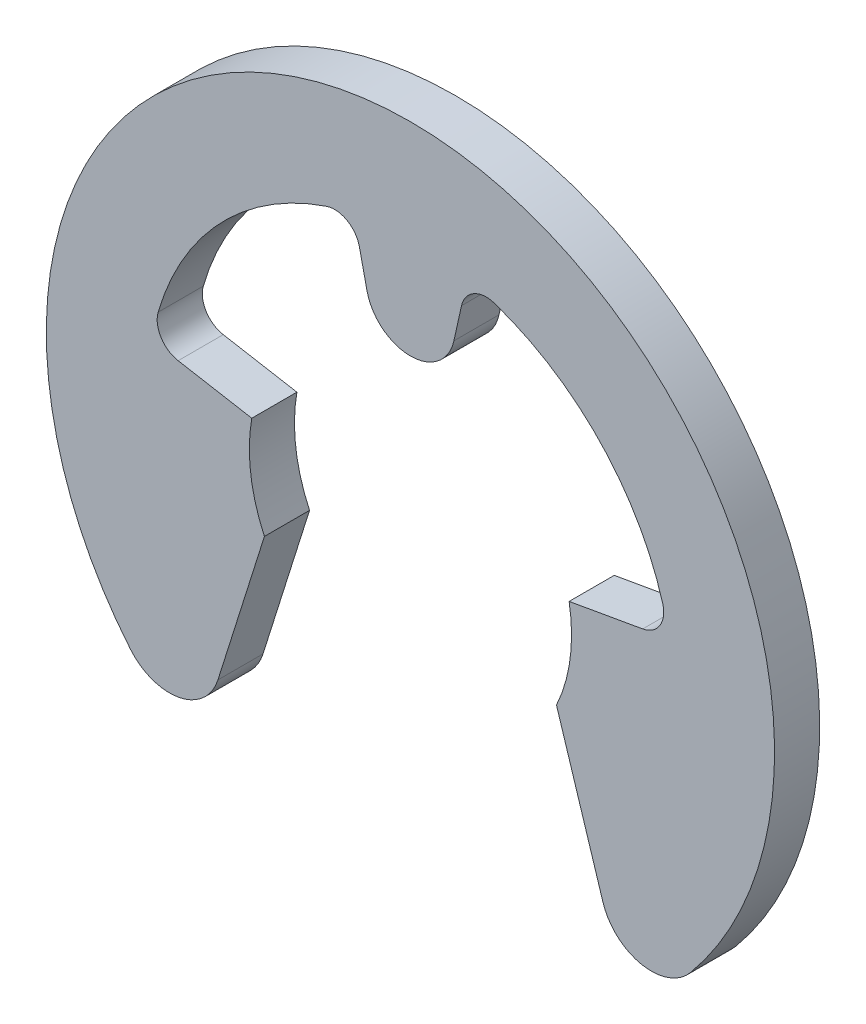
SolidWorks part; units mm, degrees
ref_plane "Plane1" through (0, 0, 0) normal (0, 0, 1) x (1, 0, 0)
ref_plane "Plane2" through (0, 0, 0) normal (0, 1, 0) x (1, 0, 0)
ref_plane "Plane3" through (0, 0, 0) normal (1, 0, 0) x (0, 0, -1)
sketch "BodySke" plane through (0, 0, 0) normal (0, 0, 1) x (1, 0, 0)
  line L0 (-0.7581, 0) -> (0.7581, 0) construction
  line L1 (0, 0) -> (0, 5.65) construction
  line L2 (0, 0) -> (0.1641, 0.7402) construction
  line L3 (0, 0) -> (5.1206, -2.3878) construction
  line L4 (0, 0) -> (-0.1641, 0.7402) construction
  line L5 (0, 0) -> (-5.1206, -2.3878) construction
  line L6 (2.462, 0.4341) -> (3.6045, 0.6356)
  line L7 (-2.462, 0.4341) -> (-3.6045, 0.6356)
  line L8 (0, 0) -> (5.5642, 0.9811) construction
  line L9 (2.2658, -1.0565) -> (2.9876, -3.3459)
  line L10 (-2.2658, -1.0565) -> (-2.9876, -3.3459)
  line L11 (0.6742, 3.0411) -> (0.7922, 3.5734)
  line L12 (-0.6742, 3.0411) -> (-0.7922, 3.5734)
  line L13 (0, 0) -> (-5.5642, 0.9811) construction
  circle A0 centre (0, 0) radius 2.5 construction
  arc A1 (3.9144, 1.1328) -> (1.3025, 3.8612) centre (0, 0) ccw
  arc A2 (4.3441, -3.6126) -> (-4.3441, -3.6126) centre (0, 0) ccw
  arc A3 (2.2658, -1.0565) -> (2.462, 0.4341) centre (0, 0) ccw
  arc A4 (-1.3025, 3.8612) -> (-3.9144, 1.1328) centre (0, 0) ccw
  arc A5 (3.6045, 0.6356) -> (3.9144, 1.1328) centre (3.5362, 1.0233) ccw
  arc A7 (1.3025, 3.8612) -> (0.7922, 3.5734) centre (1.1766, 3.4881) ccw
  arc A8 (-2.462, 0.4341) -> (-2.2658, -1.0565) centre (0, 0) ccw
  arc A9 (-3.9144, 1.1328) -> (-3.6045, 0.6356) centre (-3.5362, 1.0233) ccw
  arc A10 (-0.6742, 3.0411) -> (0.6742, 3.0411) centre (0, 3.1906) ccw
  arc A11 (-0.7922, 3.5734) -> (-1.3025, 3.8612) centre (-1.1766, 3.4881) ccw
  arc A12 (-4.3441, -3.6126) -> (-2.9876, -3.3459) centre (-3.7386, -3.1091) ccw
  arc A13 (2.9876, -3.3459) -> (4.3441, -3.6126) centre (3.7386, -3.1091) ccw
  dimension "OutsideDia" = 11.3
  dimension "CavityDia" = 8.15
  dimension "TipRad" = 0.7875
  dimension "CavityFilletRad" = 0.3938
  dimension "GrooveDia" = 5
  dimension "D3" = 25
  dimension "D4" = 35
  dimension "D1" = 35
  dimension "D2" = 160
extrude "Body" add sketch "BodySke" against normal blind 0.7
equation "' \"Thickness@Body\" = 0.2"
equation "' \"GrooveDia@BodySke\" = 0.8"
equation "' \"OutsideDia@BodySke\" = 2.25"
equation "' \"Thickness@Body\" = 2.5"
equation "' \"GrooveDia@BodySke\" = 30"
equation "' \"OutsideDia@BodySke\" = 52.6"
equation "\"CavityDia@BodySke\" = (\"OutsideDia@BodySke\"  + \"GrooveDia@BodySke\") / 2 "
equation "\"CavityFilletRad@BodySke\" =  (\"CavityDia@BodySke\" - \"GrooveDia@BodySke\") / 2 * 0.25"
equation "\"TipRad@BodySke\" = (\"OutsideDia@BodySke\"  - \"GrooveDia@BodySke\") / 2 * 0.25"
